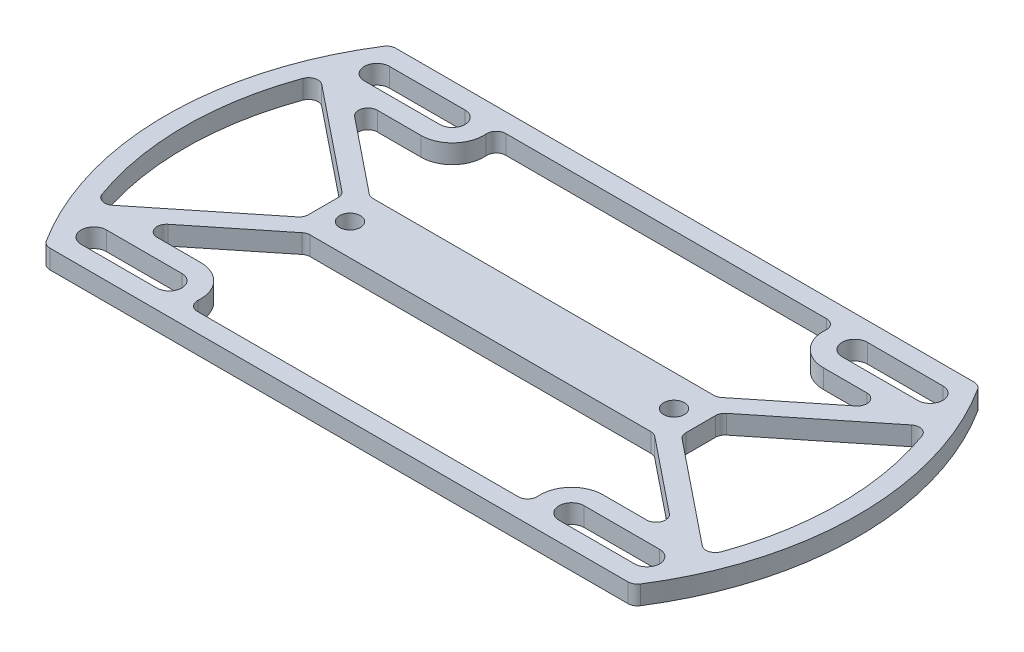
SolidWorks part; units mm, degrees
material "3.1355 (EN-AW 2024)"
ref_plane "Front" through (0, 0, 0) normal (0, 0, 1) x (1, 0, 0)
ref_plane "Top" through (0, 0, 0) normal (0, 1, 0) x (1, 0, 0)
ref_plane "Right" through (0, 0, 0) normal (1, 0, 0) x (0, 0, -1)
sketch "Эскиз1" plane through (0, 0, 0) normal (0, 1, 0) x (1, 0, 0)
  line L0 (9.8908, 3) -> (100.1092, 3)
  line L1 (0, 0) -> (8.2418, 0) construction
  line L2 (0, 0) -> (0, 55) construction
  line L3 (0, 55) -> (8.2418, 55) construction
  line L4 (110, 0) -> (110, 55) construction
  line L5 (9.8908, 52) -> (100.1092, 52)
  line L8 (110, 27.5) -> (0, 27.5) construction
  line L9 (8.2418, 0) -> (101.7582, 0)
  line L11 (8.2418, 55) -> (101.7582, 55)
  line L13 (55, 55) -> (55, 0) construction
  arc A0 (8.2418, 55) -> (8.2418, 0) centre (50, 27.5) ccw
  arc A1 (101.7582, 55) -> (101.7582, 0) centre (60, 27.5) cw
  arc A2 (9.8908, 52) -> (9.8908, 3) centre (50, 27.5) ccw
  arc A3 (100.1092, 52) -> (100.1092, 3) centre (60, 27.5) cw
  point P14 (55, 27.5)
  point P20 (55, 55)
  point P22 (55, 0)
  dimension "D4" = 50
  dimension "D1" = 55
  dimension "D2" = 110
  dimension "D3" = 3
extrude "Бобышка-Вытянуть1" add sketch "Эскиз1" along normal blind 3
sketch "Эскиз3" plane through (0, 0, 0) normal (0, -1, 0) x (1, 0, 0)
  line L0 (25, -32.5) -> (85, -22.5) construction
  line L1 (85, -32.5) -> (25, -32.5)
  line L2 (85, -32.5) -> (85, -22.5)
  line L3 (85, -22.5) -> (25, -22.5)
  line L4 (25, -32.5) -> (25, -22.5)
  line L5 (55, 0) -> (55, -55) construction
  line L10 (8.2418, 0) -> (101.7582, 0) construction
  line L11 (101.7582, -55) -> (8.2418, -55) construction
  point P10 (55, -27.5)
  dimension "D1" = 10
  dimension "D2" = 60
extrude "Бобышка-Вытянуть3" add sketch "Эскиз3" against normal through all separate body
sketch "Эскиз4" plane through (0, 0, 0) normal (0, -1, 0) x (1, 0, 0)
  line L0 (11.0289, -5) -> (23.0289, -5) construction
  line L1 (11.0289, -3) -> (23.0289, -3)
  line L2 (11.0289, -7) -> (23.0289, -7)
  line L3 (9.8908, -3) -> (100.1092, -3) construction
  line L4 (55, 0) -> (55, -55) construction
  line L5 (8.2418, 0) -> (101.7582, 0) construction
  line L6 (101.7582, -55) -> (8.2418, -55) construction
  line L7 (0, -27.5) -> (110, -27.5) construction
  line L8 (11.0289, -3) -> (9.8908, -3)
  line L9 (11.0289, -10) -> (23.0289, -10)
  line L10 (9.8908, -3) -> (27.6114, -3)
  line L11 (11.0289, 0) -> (23.0289, 0) construction
  line L12 (98.9711, -5) -> (86.9711, -5) construction
  line L13 (98.9711, -3) -> (86.9711, -3)
  line L14 (98.9711, -7) -> (86.9711, -7)
  line L15 (100.1092, -3) -> (82.3886, -3)
  line L16 (98.9711, -10) -> (86.9711, -10)
  line L17 (98.9711, -3) -> (100.1092, -3)
  line L18 (11.0289, -50) -> (23.0289, -50) construction
  line L19 (11.0289, -52) -> (23.0289, -52)
  line L20 (11.0289, -48) -> (23.0289, -48)
  line L21 (98.9711, -50) -> (86.9711, -50) construction
  line L22 (98.9711, -52) -> (86.9711, -52)
  line L23 (98.9711, -48) -> (86.9711, -48)
  line L24 (98.9711, -52) -> (100.1092, -52)
  line L25 (98.9711, -45) -> (86.9711, -45)
  line L26 (100.1092, -52) -> (82.3886, -52)
  line L27 (9.8908, -52) -> (27.6114, -52)
  line L28 (11.0289, -45) -> (23.0289, -45)
  line L29 (11.0289, -52) -> (9.8908, -52)
  arc A0 (11.0289, -3) -> (11.0289, -7) centre (11.0289, -5) ccw
  arc A1 (23.0289, -7) -> (23.0289, -3) centre (23.0289, -5) ccw
  arc A2 (9.8908, -3) -> (9.8908, -52) centre (50, -27.5) ccw construction
  arc A3 (8.2418, 0) -> (8.2418, -55) centre (50, -27.5) ccw construction
  arc A4 (101.7582, -55) -> (101.7582, 0) centre (60, -27.5) ccw construction
  arc A5 (23.0289, -10) -> (27.6114, -3) centre (23.0289, -5) ccw
  arc A6 (7.1601, -8.1675) -> (11.0289, -10) centre (11.0289, -5) ccw
  arc A7 (9.8908, -3) -> (7.1601, -8.1675) centre (50, -27.5) ccw
  arc A8 (98.9711, -3) -> (98.9711, -7) centre (98.9711, -5) cw
  arc A9 (11.0289, 0) -> (11.0289, -10) centre (11.0289, -5) ccw construction
  arc A10 (23.0289, -10) -> (23.0289, 0) centre (23.0289, -5) ccw construction
  arc A11 (86.9711, -7) -> (86.9711, -3) centre (86.9711, -5) cw
  arc A12 (100.1092, -3) -> (102.8399, -8.1675) centre (60, -27.5) cw
  arc A13 (102.8399, -8.1675) -> (98.9711, -10) centre (98.9711, -5) cw
  arc A14 (86.9711, -10) -> (82.3886, -3) centre (86.9711, -5) cw
  arc A15 (11.0289, -52) -> (11.0289, -48) centre (11.0289, -50) cw
  arc A16 (23.0289, -48) -> (23.0289, -52) centre (23.0289, -50) cw
  arc A17 (98.9711, -52) -> (98.9711, -48) centre (98.9711, -50) ccw
  arc A18 (86.9711, -48) -> (86.9711, -52) centre (86.9711, -50) ccw
  arc A19 (86.9711, -45) -> (82.3886, -52) centre (86.9711, -50) ccw
  arc A20 (102.8399, -46.8325) -> (98.9711, -45) centre (98.9711, -50) ccw
  arc A21 (100.1092, -52) -> (102.8399, -46.8325) centre (60, -27.5) ccw
  arc A22 (9.8908, -52) -> (7.1601, -46.8325) centre (50, -27.5) cw
  arc A23 (7.1601, -46.8325) -> (11.0289, -45) centre (11.0289, -50) cw
  arc A24 (23.0289, -45) -> (27.6114, -52) centre (23.0289, -50) cw
  point P2 (17.0289, -5)
  point P36 (92.9711, -5)
  point P51 (17.0289, -50)
  point P58 (92.9711, -50)
  arc M5 (9.8908, -52) -> (9.8908, -3) centre (50, -27.5) cw
  line M6 (9.8908, -3) -> (100.1092, -3)
  arc M7 (100.1092, -3) -> (100.1092, -52) centre (60, -27.5) cw
  line M8 (100.1092, -52) -> (9.8908, -52)
  dimension "D1" = 2
  dimension "D2" = 12
  dimension "D3" = 3
extrude "Бобышка-Вытянуть4" add sketch "Эскиз4" against normal through all contours A6 L9 A5 A1 L2 A0 M5 M6 | A0 M6 M5 | A14 L16 A13 A8 L14 A11 M7 M6 | A8 M6 M7 | A20 L25 A19 A18 L23 A17 M7 M8 | A17 M8 M7 | A24 L28 A23 A15 L20 A16 M5 M8 | A15 M8 M5
sketch "Эскиз5" plane through (0, 0, 0) normal (0, -1, 0) x (1, 0, 0)
  line L0 (25, -22.5) -> (7.1601, -8.1675) construction
  line L1 (25, -32.5) -> (7.1601, -46.8325) construction
  line L2 (102.8399, -8.1675) -> (85, -22.5) construction
  line L3 (85, -32.5) -> (85, -22.5) construction
  line L4 (85, -32.5) -> (102.8399, -46.8325) construction
  line L5 (27.395, -22.5) -> (8.0996, -6.9981)
  line L6 (25, -30.5759) -> (6.2207, -45.6631)
  line L7 (101.9004, -6.9981) -> (82.605, -22.5)
  line L8 (82.605, -32.5) -> (101.9004, -48.0019)
  line L9 (25, -24.4241) -> (6.2207, -9.3369)
  line L10 (27.395, -32.5) -> (8.0996, -48.0019)
  line L11 (103.7793, -9.3369) -> (85, -24.4241)
  line L12 (85, -30.5759) -> (103.7793, -45.6631)
  line L13 (25.9395, -21.3306) -> (8.0996, -6.9981) construction
  line L14 (24.0605, -23.6694) -> (6.2207, -9.3369) construction
  line L15 (24.0605, -31.3306) -> (6.2207, -45.6631) construction
  line L16 (25.9395, -33.6694) -> (8.0996, -48.0019) construction
  line L17 (85, -32.5) -> (85, -22.5)
  line L18 (85, -22.5) -> (25, -22.5)
  line L19 (25, -22.5) -> (25, -32.5)
  line L20 (25, -32.5) -> (85, -32.5)
  line L21 (85, -32.5) -> (85, -30.5759)
  line L22 (85, -22.5) -> (82.605, -22.5)
  line L23 (25, -22.5) -> (25, -24.4241)
  line L24 (25, -32.5) -> (27.395, -32.5)
  line L25 (84.0605, -33.6694) -> (101.9004, -48.0019) construction
  line L26 (85.9395, -31.3306) -> (103.7793, -45.6631) construction
  line L27 (103.7793, -9.3369) -> (85.9395, -23.6694) construction
  line L28 (101.9004, -6.9981) -> (84.0605, -21.3306) construction
  line L29 (27.395, -22.5) -> (25, -22.5)
  line L30 (85, -24.4241) -> (85, -22.5)
  line L31 (82.605, -32.5) -> (85, -32.5)
  line L32 (25, -30.5759) -> (25, -32.5)
  line L33 (8.0996, -6.9981) -> (6.2207, -9.3369)
  line L34 (8.0996, -48.0019) -> (6.2207, -45.6631)
  line L35 (101.9004, -48.0019) -> (103.7793, -45.6631)
  line L36 (101.9004, -6.9981) -> (103.7793, -9.3369)
  dimension "D1" = 1.5
  dimension "D2" = 1.5
  dimension "D3" = 0
extrude "Бобышка-Вытянуть5" add sketch "Эскиз5" against normal through all
fillet "Скругление1" radius 1.5 20 edges at (103.4564, 1.5, -9.5963) (103.4564, 1.5, -45.4037) (85, 1.5, -24.4241) (85, 1.5, -30.5759) (25, 1.5, -24.4241) (25, 1.5, -30.5759) (6.5436, 1.5, -9.5963) (6.5436, 1.5, -45.4037) (27.6114, 1.5, -52) (11.8361, 1.5, -45) (82.3886, 1.5, -52) (98.1639, 1.5, -45) (82.605, 1.5, -32.5) (27.395, 1.5, -32.5) (82.605, 1.5, -22.5) (98.1639, 1.5, -10) (82.3886, 1.5, -3) (27.6114, 1.5, -3) (27.395, 1.5, -22.5) (11.8361, 1.5, -10)
fillet "Скругление2" radius 1.5 4 edges at (8.2418, 1.5, 0) (8.2418, 1.5, -55) (101.7582, 1.5, 0) (101.7582, 1.5, -55)
hole_wizard "Отверстие обработанное метчиком M4x0.71" positions "Эскиз6" profile "Эскиз7" tap size "M4x0.7" standard "Ansi Metric" end condition through all
sketch "Эскиз6" plane through (-0.1211, 0, 3.1982) normal (0, -1, 0) x (-1, 0, 0)
  point P0 (-80.8711, 30.6982)
  point P3 (-29.3711, 30.6982)
sketch "Эскиз7" plane through (80.75, 0, -27.5) normal (1, 0, 0) x (0, 0, -1)
  line L0 (0, 0) -> (0, 3)
  line L1 (0, 3) -> (1.65, 3)
  line L2 (1.65, 3) -> (1.65, 0)
  line L3 (1.65, 0) -> (0, 0)
  line L4 (0, -6.35) -> (0, 107.95) construction
  dimension "Диаметр проходного сверла" = 3.3
  dimension "Глубина проходного сверла" = 3
cosmetic thread "Отверстие резьбы1" parameters "D2"=4
cosmetic thread "Отверстие резьбы2" parameters "D2"=4
